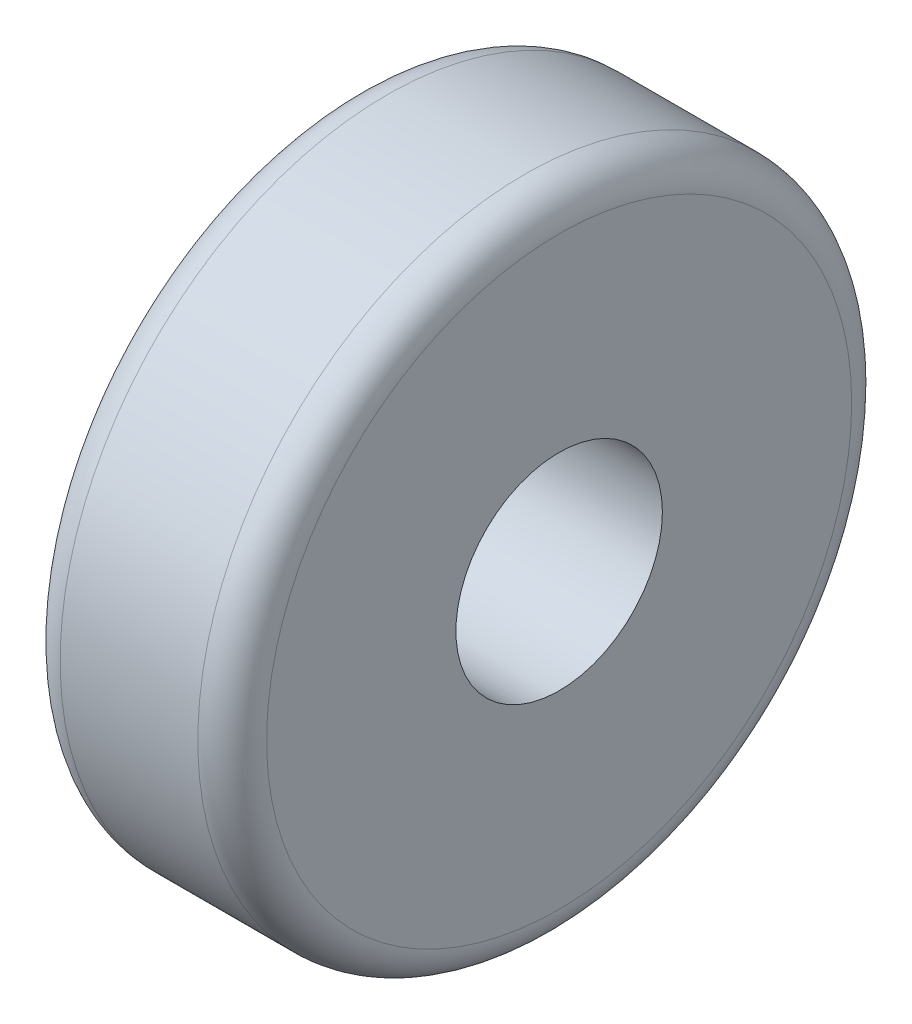
SolidWorks part; units mm, degrees
ref_plane "前视基准面" through (0, 0, 0) normal (0, 0, 1) x (1, 0, 0)
ref_plane "上视基准面" through (0, 0, 0) normal (0, 1, 0) x (1, 0, 0)
ref_plane "右视基准面" through (0, 0, 0) normal (1, 0, 0) x (0, 0, -1)
sketch "草图1" plane through (0, 0, 0) normal (1, 0, 0) x (0, 0, -1)
  circle A0 centre (0, 0) radius 3
  circle A1 centre (0, 0) radius 9.5
extrude "凸台-拉伸1" add sketch "草图1" along normal blind 6
fillet "圆角1" radius 1 2 edges at (6, 0, -9.5) (0, 0, -9.5)
